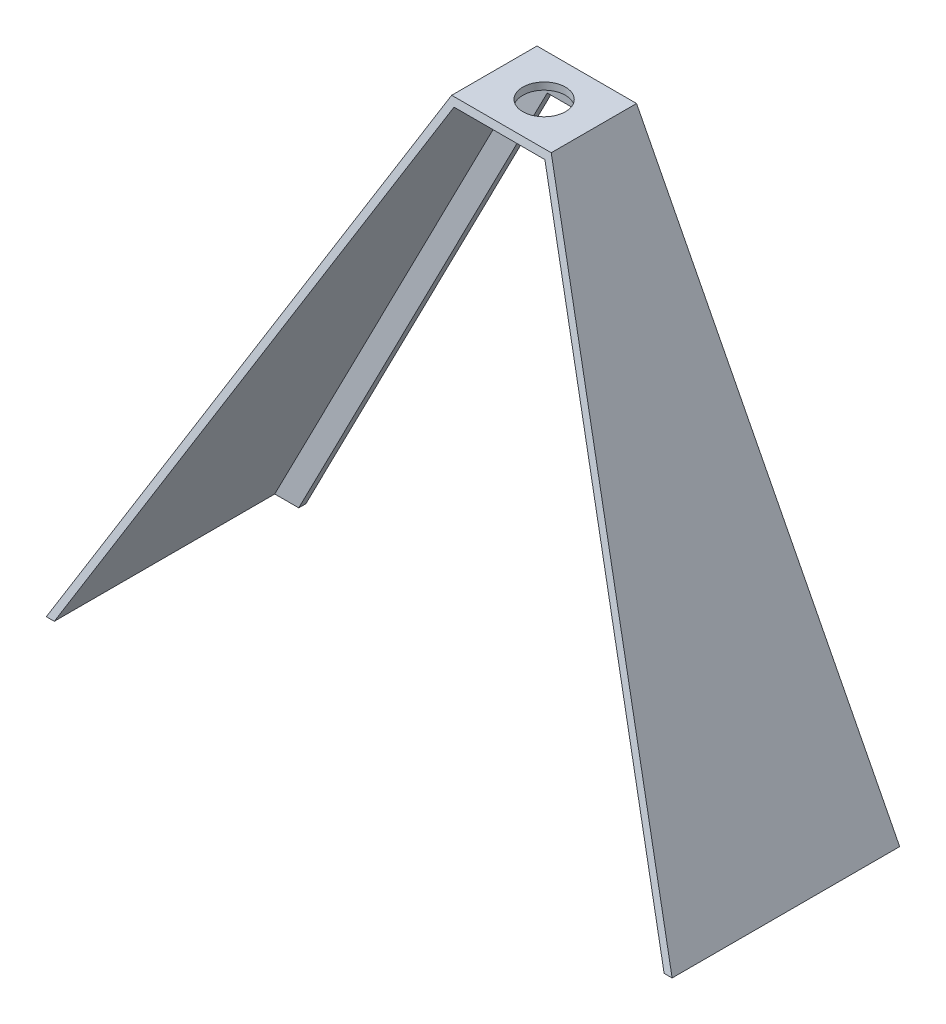
SolidWorks part; units mm, degrees
ref_plane "Front Plane" through (0, 0, 0) normal (0, 0, 1) x (1, 0, 0)
ref_plane "Top Plane" through (0, 0, 0) normal (0, 1, 0) x (1, 0, 0)
ref_plane "Right Plane" through (0, 0, 0) normal (1, 0, 0) x (0, 0, -1)
sketch "Sketch1" plane through (0, 0, 0) normal (0, 0, 1) x (1, 0, 0)
  line L0 (-279.4, 0) -> (-44.45, 457.2)
  line L1 (-44.45, 457.2) -> (44.45, 457.2)
  line L2 (44.45, 457.2) -> (279.4, 0)
  line L3 (279.4, 0) -> (-279.4, 0)
  point P3 (0, 0)
  dimension "D1" = 558.8
  dimension "D2" = 88.9
  dimension "D3" = 457.2
extrude "Boss-Extrude1" add sketch "Sketch1" along normal blind 203.2
sketch "Sketch2" plane through (0, 0, 0) normal (1, 0, 0) x (0, 0, -1)
  line L0 (-203.2, 0) -> (-76.2, 457.2)
  line L1 (-203.2, 457.2) -> (0, 457.2) construction
  line L2 (-76.2, 457.2) -> (-203.2, 457.2)
  line L3 (-203.2, 457.2) -> (-203.2, 0)
  dimension "D1" = 76.2
extrude "Cut-Extrude1" cut sketch "Sketch2" against normal through all both and the other way through all
shell "Shell1" thickness 6.35
sketch "Sketch3" plane through (0, 0, 0) normal (0, 0, -1) x (-1, 0, 0)
  line L0 (-28.9452, 431.8) -> (-250.8424, 0)
  line L1 (-250.8424, 0) -> (250.8424, 0)
  line L2 (250.8424, 0) -> (28.9452, 431.8)
  line L3 (28.9452, 431.8) -> (-28.9452, 431.8)
  line L4 (-279.4, 0) -> (279.4, 0)
  line L5 (279.4, 0) -> (44.45, 457.2)
  line L6 (44.45, 457.2) -> (-44.45, 457.2)
  line L7 (-44.45, 457.2) -> (-279.4, 0)
  line L8 (-279.4, 0) -> (279.4, 0)
  line L9 (279.4, 0) -> (44.45, 457.2)
  line L10 (44.45, 457.2) -> (-44.45, 457.2)
  line L11 (-44.45, 457.2) -> (-279.4, 0)
  dimension "D2" = 25.4
  dimension "D3" = 25.4
  dimension "D4" = 25.4
  dimension "D1" = 0
extrude "Cut-Extrude2" cut sketch "Sketch3" against normal through all contours L2 L3 L0 L1
sketch "Sketch4" plane through (0, 457.2, 0) normal (0, 1, 0) x (1, 0, 0)
  line L0 (44.45, -76.2) -> (-44.45, 0) construction
  circle A0 centre (0, -38.1) radius 19.05
  dimension "D1" = 38.1
extrude "Cut-Extrude3" cut sketch "Sketch4" against normal through all
